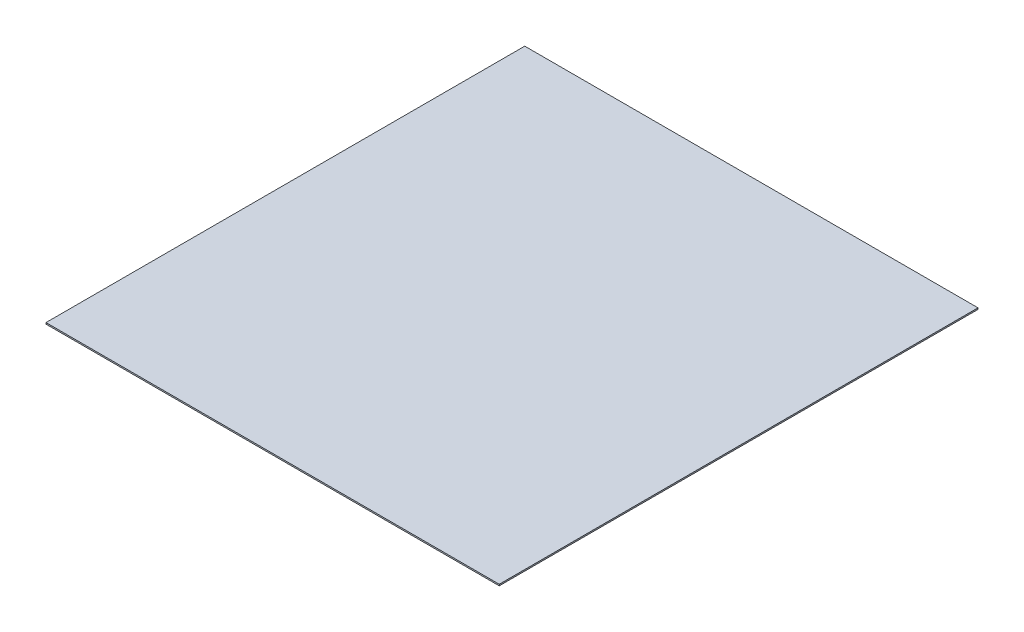
SolidWorks part; units mm, degrees
material "Pine"
ref_plane "Front Plane" through (0, 0, 0) normal (0, 0, 1) x (1, 0, 0)
ref_plane "Top Plane" through (0, 0, 0) normal (0, 1, 0) x (1, 0, 0)
ref_plane "Right Plane" through (0, 0, 0) normal (1, 0, 0) x (0, 0, -1)
sketch "Sketch1" plane through (0, 0, 0) normal (0, 1, 0) x (1, 0, 0)
  line L1 (0, 0) -> (1016, 0)
  line L2 (0, 0) -> (0, 1073.15)
  line L3 (0, 1073.15) -> (1016, 1073.15)
  line L4 (1016, 0) -> (1016, 1073.15)
  dimension "D1" = 1016
  dimension "D2" = 1073.15
extrude "Boss-Extrude1" add sketch "Sketch1" along normal blind 3.175
